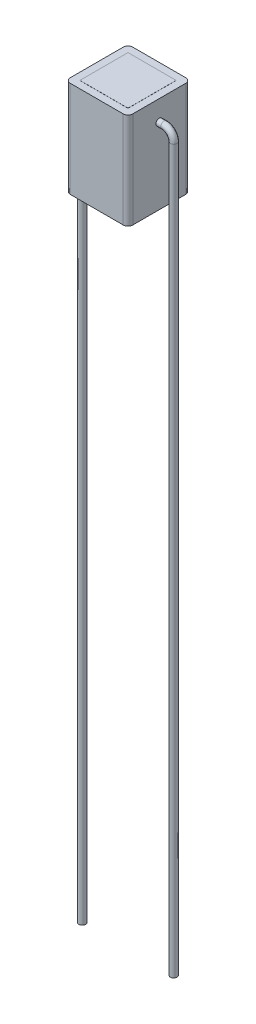
SolidWorks part; units mm, degrees
ref_plane "Front Plane" through (0, 0, 0) normal (0, 0, 1) x (1, 0, 0)
ref_plane "Top Plane" through (0, 0, 0) normal (0, 1, 0) x (1, 0, 0)
ref_plane "Right Plane" through (0, 0, 0) normal (1, 0, 0) x (0, 0, -1)
sketch "Sketch1" plane through (0, 0, 0) normal (0, 1, 0) x (1, 0, 0)
  line L1 (-3.25, 3.25) -> (3.25, 3.25)
  line L2 (-3.25, 3.25) -> (-3.25, -3.25)
  line L3 (-3.25, -3.25) -> (3.25, -3.25)
  line L4 (3.25, 3.25) -> (3.25, -3.25)
  line L5 (-3.25, 3.25) -> (3.25, -3.25) construction
  line L6 (-3.25, -3.25) -> (3.25, 3.25) construction
  point P0 (0, 0)
sketch "Sketch2" plane through (0, 0, 0) normal (0, 1, 0) x (1, 0, 0)
  line L1 (-2.5, 2.5) -> (2.5, 2.5)
  line L2 (-2.5, 2.5) -> (-2.5, -2.5)
  line L3 (-2.5, -2.5) -> (2.5, -2.5)
  line L4 (2.5, 2.5) -> (2.5, -2.5)
  line L5 (-2.5, 2.5) -> (2.5, -2.5) construction
  line L6 (-2.5, -2.5) -> (2.5, 2.5) construction
  point P0 (0, 0)
extrude "Boss-Extrude1" add sketch "Sketch1" along normal blind 10
extrude "Boss-Extrude2" add sketch "Sketch2" along normal blind 10.01 and the other way blind 0.01
sketch "Sketch3" plane through (3.25, 0, 0) normal (1, 0, 0) x (0, 0, -1)
  circle A0 centre (0, 7.8829) radius 1
sketch "Sketch4" plane through (0, 0, 0) normal (0, 0, 1) x (1, 0, 0)
  line L0 (3.25, 7.8829) -> (3.2, 7.8829)
  line L1 (3.25, 7.8829) -> (3.75, 7.8829)
  line L2 (4.75, 6.8829) -> (4.75, -68.1171)
  arc A0 (3.75, 7.8829) -> (4.75, 6.8829) centre (3.75, 6.8829) cw
  dimension "D1" = 1
sweep "Sweep2" add path "Sketch4" circular profile diameter 0.7 parameters "D3"=0.7
mirror "Mirror1" about plane through (0, 0, 0) normal (1, 0, 0) of "Boss-Extrude1", "Sweep2"
fillet "Fillet2" radius 0.5 4 edges at (3.25, 5, 3.25) (-3.25, 5, 3.25) (-3.25, 5, -3.25) (3.25, 5, -3.25)
